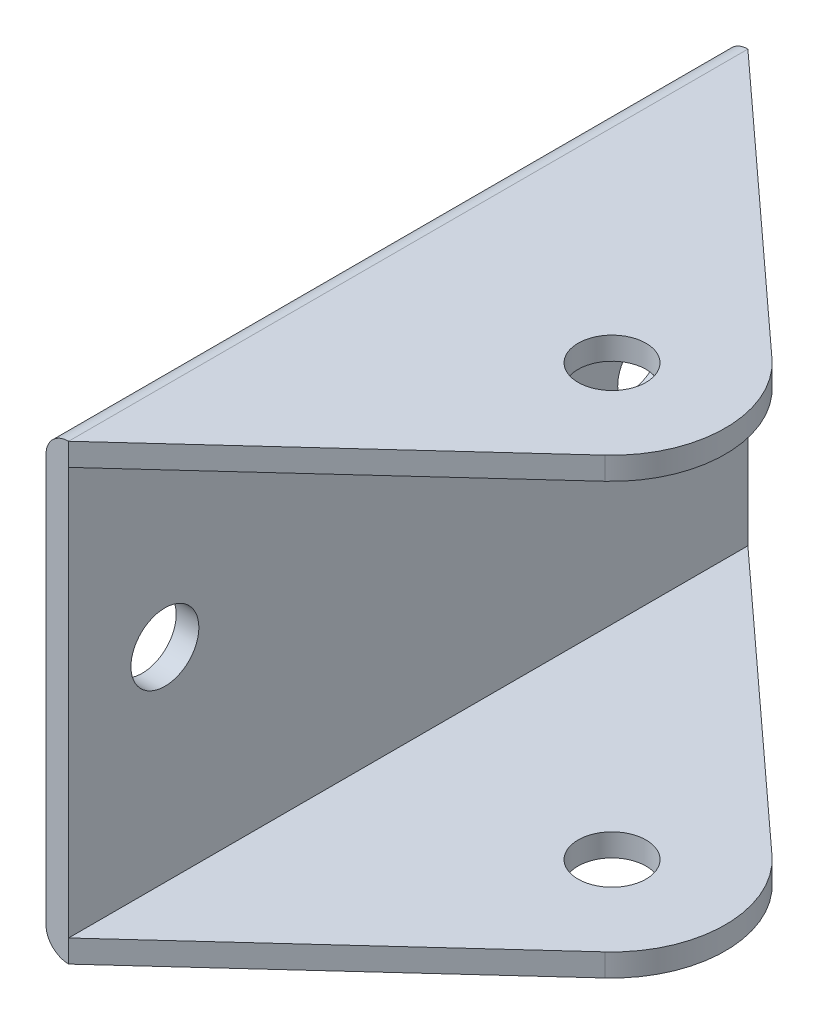
SolidWorks part; units mm, degrees
ref_plane "Спереди" through (0, 0, 0) normal (0, 0, 1) x (1, 0, 0)
ref_plane "Сверху" through (0, 0, 0) normal (0, 1, 0) x (1, 0, 0)
ref_plane "Справа" through (0, 0, 0) normal (1, 0, 0) x (0, 0, -1)
other "Configuration Table"
sketch "Эскиз1" plane through (0, 0, 0) normal (0, 0, 1) x (1, 0, 0)
  line L1 (-18, 18) -> (18, 18)
  line L2 (-18, 18) -> (-18, -18)
  line L3 (-18, -18) -> (18, -18)
  line L4 (18, 18) -> (18, -18)
  line L5 (-18, 18) -> (18, -18) construction
  line L6 (-18, -18) -> (18, 18) construction
  line L7 (-18, 20) -> (18, 20)
  line L8 (-20, 18) -> (-20, -18)
  line L9 (-18, -20) -> (18, -20)
  line L10 (20, 18) -> (20, -18)
  line L11 (-20, 20) -> (20, -20) construction
  line L12 (-20, -20) -> (20, 20) construction
  arc A0 (-20, -18) -> (-18, -20) centre (-18, -18) ccw
  arc A1 (18, 20) -> (20, 18) centre (18, 18) cw
  arc A2 (18, -20) -> (20, -18) centre (18, -18) ccw
  arc A3 (-18, 20) -> (-20, 18) centre (-18, 18) ccw
  point P0 (0, 0)
  point P6 (0, 0)
  dimension "D4" = 2
  dimension "D1" = 2
  dimension "D2" = 2
  dimension "D3" = 40
extrude "Бобышка-Вытянуть1" add sketch "Эскиз1" along normal blind 100
sketch "Эскиз2" plane through (0, 20, 0) normal (0, 1, 0) x (1, 0, 0)
  line L0 (-20, -50) -> (20, -50) construction
  line L1 (-20, -100) -> (-20, 0) construction
  line L2 (20, -100) -> (20, 0) construction
  circle A0 centre (0, -50) radius 3
  dimension "D1" = 6
extrude "Вырез-Вытянуть1" cut sketch "Эскиз2" against normal through all both and the other way through all
sketch "Эскиз3" plane through (0, 20, 0) normal (0, 1, 0) x (1, 0, 0)
  line L0 (0, -50) -> (-20, -50) construction
  line L1 (-20, -100) -> (-20, 0) construction
  line L2 (6.7466, -42.6187) -> (-18, -20)
  line L3 (-18, -100) -> (-18, 0) construction
  line L4 (-18, -20) -> (-21.8374, -20)
  line L5 (-21.8374, -20) -> (-21.8374, -80)
  line L6 (-21.8374, -80) -> (-18, -80)
  line L7 (-18, -80) -> (6.7466, -57.3813)
  arc A0 (6.7466, -42.6187) -> (6.7466, -57.3813) centre (0, -50) cw
  dimension "D2" = 10
  dimension "D1" = 60
extrude "Вырез-Вытянуть2" cut sketch "Эскиз3" against normal through all both and the other way through all flip side to cut
sketch "Эскиз4" plane through (-18, 0, 0) normal (1, 0, 0) x (0, 0, -1)
  line L0 (-80, 0) -> (-20, 0) construction
  line L1 (-80, -18) -> (-80, 18) construction
  line L2 (-20, -18) -> (-20, 18) construction
  line L3 (-50, 0) -> (-50, 18) construction
  line L4 (-80, 18) -> (-20, 18) construction
  circle A0 centre (-71.5, 0) radius 3
  circle A1 centre (-28.5, 0) radius 3
  circle A2 centre (-28.5, 0) radius 8 construction
  dimension "D1" = 6
  dimension "D3" = 16
  dimension "D2" = 43
extrude "Вырез-Вытянуть3" cut sketch "Эскиз4" against normal through all both and the other way through all
